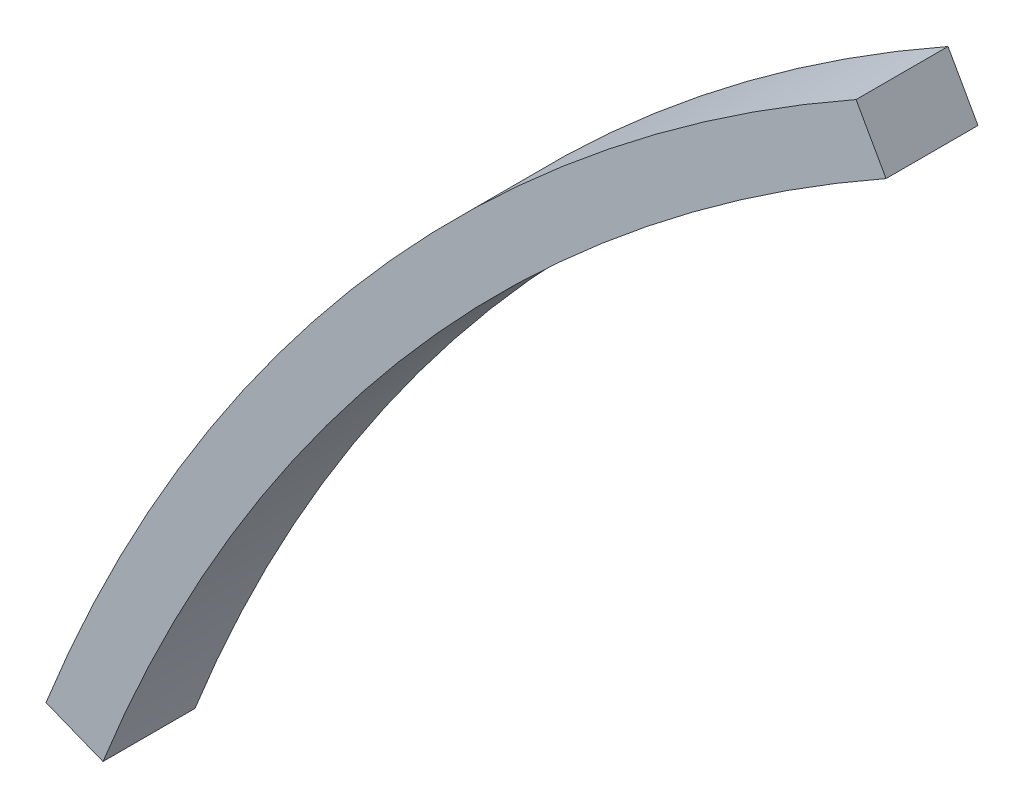
SolidWorks part; units mm, degrees
ref_plane "Front Plane" through (0, 0, 0) normal (0, 0, 1) x (1, 0, 0)
ref_plane "Top Plane" through (0, 0, 0) normal (0, 1, 0) x (1, 0, 0)
ref_plane "Right Plane" through (0, 0, 0) normal (1, 0, 0) x (0, 0, -1)
sketch "Sketch1" plane through (0, 0, 0) normal (0, 0, 1) x (1, 0, 0)
  line L0 (-53.9345, 21.3323) -> (-55.7943, 22.0679)
  line L1 (-28.3843, 50.58) -> (-29.363, 52.3241)
  arc A0 (-29.363, 52.3241) -> (-55.7943, 22.0679) centre (0, 0) ccw
  arc A1 (-28.3843, 50.58) -> (-53.9345, 21.3323) centre (0, 0) ccw
  dimension "D1" = 116
  dimension "120" = 120
extrude "Boss-Extrude1" add sketch "Sketch1" along normal blind 3
